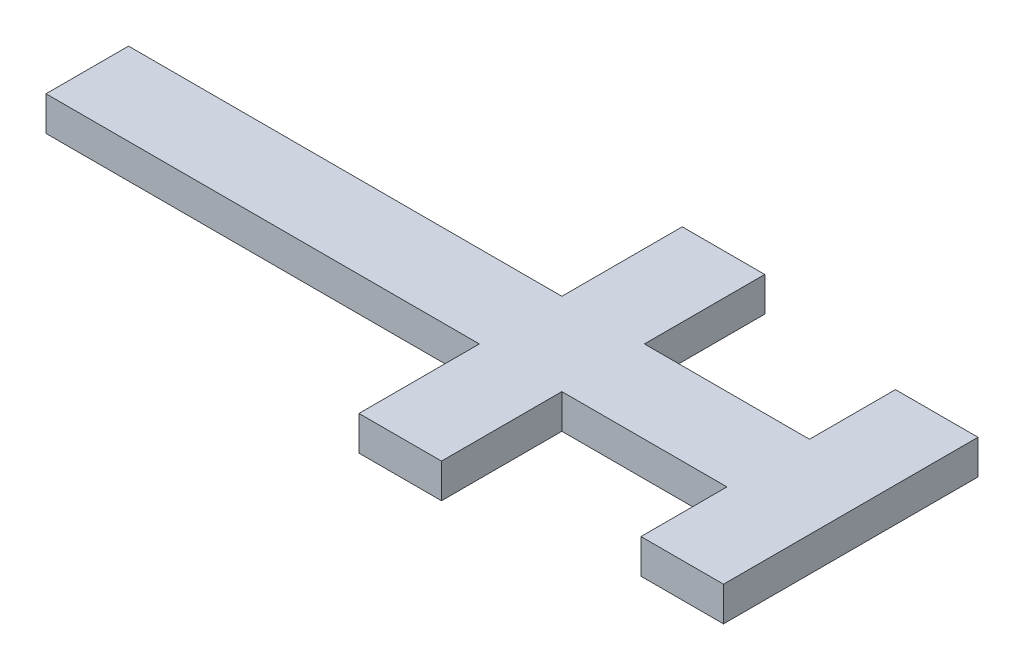
SolidWorks part; units mm, degrees
ref_plane "前视基准面" through (0, 0, 0) normal (0, 0, 1) x (1, 0, 0)
ref_plane "上视基准面" through (0, 0, 0) normal (0, 1, 0) x (1, 0, 0)
ref_plane "右视基准面" through (0, 0, 0) normal (1, 0, 0) x (0, 0, -1)
other "Configuration Table"
sketch "草图2" plane through (0, 0, 0) normal (0, 1, 0) x (1, 0, 0)
  line L0 (0, 0) -> (-40, 0) construction
  line L5 (-14, -5) -> (14, -5)
  line L6 (-14, -5) -> (-14, 5)
  line L7 (-14, 5) -> (14, 5)
  line L8 (14, -5) -> (14, 5)
  line L9 (-14, -5) -> (14, 5) construction
  line L10 (-14, 5) -> (14, -5) construction
  line L11 (19, 0) -> (14, 0) construction
  line L12 (-20, -5) -> (-60, -5)
  line L13 (-20, -5) -> (-20, 5)
  line L14 (-20, 5) -> (-60, 5)
  line L15 (-60, -5) -> (-60, 5)
  line L16 (-20, -5) -> (-60, 5) construction
  line L17 (-20, 5) -> (-60, -5) construction
  line L18 (-12, -22.5) -> (-22, -22.5)
  line L19 (-12, -22.5) -> (-12, 22.5)
  line L20 (-12, 22.5) -> (-22, 22.5)
  line L21 (-22, -22.5) -> (-22, 22.5)
  line L22 (-12, -22.5) -> (-22, 22.5) construction
  line L23 (-12, 22.5) -> (-22, -22.5) construction
  line L24 (24, -17.5) -> (14, -17.5)
  line L25 (24, -17.5) -> (24, 17.5)
  line L26 (24, 17.5) -> (14, 17.5)
  line L27 (14, -17.5) -> (14, 17.5)
  line L28 (24, -17.5) -> (14, 17.5) construction
  line L29 (24, 17.5) -> (14, -17.5) construction
  line L31 (-60, 5) -> (-85, 5)
  line L32 (-60, 5) -> (-60, -5)
  line L33 (-60, -5) -> (-85, -5)
  line L34 (-85, 5) -> (-85, -5)
  point P0 (0, 0)
  point P13 (19, 0)
  point P15 (-17, 0)
  dimension "D1" = 10
  dimension "D2" = 28
  dimension "D3" = 40
  dimension "D4" = 10
  dimension "D5" = 40
  dimension "D6" = 10
  dimension "D7" = 3
  dimension "D8" = 45
  dimension "D9" = 10
  dimension "D10" = 5
  dimension "D11" = 35
  dimension "D12" = 25
sketch "草图3" plane through (0, 0, 0) normal (0, 1, 0) x (1, 0, 0)
  line L0 (-14, -5) -> (14, -5) construction
  line L1 (24, 17.5) -> (14, 17.5)
  line L2 (24, 17.5) -> (24, -17.5)
  line L3 (24, -17.5) -> (14, -17.5)
  line L4 (14, 17.5) -> (14, -17.5)
  line L5 (14, 5) -> (-12, 5)
  line L6 (14, 5) -> (14, -5)
  line L7 (14, -5) -> (-12, -5)
  line L8 (-12, 5) -> (-12, -5)
  line L9 (-12, -22.5) -> (-12, 22.5) construction
  line L10 (-20, 5) -> (-60, 5) construction
  line L11 (-12, 22.5) -> (-22, 22.5)
  line L12 (-12, 22.5) -> (-12, -22.5)
  line L13 (-12, -22.5) -> (-22, -22.5)
  line L14 (-22, 22.5) -> (-22, -22.5)
  line L15 (-60, -5) -> (-22, -5)
  line L16 (-60, -5) -> (-60, 5)
  line L17 (-60, 5) -> (-22, 5)
  line L18 (-22, -5) -> (-22, 5)
  line L20 (-60, 5) -> (-85, 5)
  line L21 (-60, 5) -> (-60, -5)
  line L22 (-60, -5) -> (-85, -5)
  line L23 (-85, 5) -> (-85, -5)
extrude "凸台-拉伸1" add sketch "草图3" along normal blind 1 contours L1 L4 L3 L2 | L5 L8 L7 L4 | L11 L14 L13 L12 L8 | L17 L16 L15 L14 | L20 L23 L22 L16
sketch "草图4" plane through (0, 0, 0) normal (0, -1, 0) x (1, 0, 0)
  line L0 (13, -18.5) -> (25, -18.5)
  line L1 (25, -18.5) -> (25, 18.5)
  line L2 (25, 18.5) -> (13, 18.5)
  line L3 (13, 18.5) -> (13, 6)
  line L4 (13, 6) -> (-11, 6)
  line L5 (-11, 6) -> (-11, 23.5)
  line L6 (-11, 23.5) -> (-23, 23.5)
  line L7 (-23, 23.5) -> (-23, 6)
  line L8 (-23, 6) -> (-86, 6)
  line L9 (-86, 6) -> (-86, -6)
  line L10 (-86, -6) -> (-23, -6)
  line L11 (-23, -6) -> (-23, -23.5)
  line L12 (-23, -23.5) -> (-11, -23.5)
  line L13 (-11, -23.5) -> (-11, -6)
  line L14 (-11, -6) -> (13, -6)
  line L15 (13, -6) -> (13, -18.5)
  line L16 (14, -17.5) -> (24, -17.5)
  line L17 (24, -17.5) -> (24, 17.5)
  line L18 (24, 17.5) -> (14, 17.5)
  line L19 (14, 17.5) -> (14, 5)
  line L20 (14, 5) -> (-12, 5)
  line L21 (-12, 5) -> (-12, 22.5)
  line L22 (-12, 22.5) -> (-22, 22.5)
  line L23 (-22, 22.5) -> (-22, 5)
  line L24 (-22, 5) -> (-85, 5)
  line L25 (-85, 5) -> (-85, -5)
  line L26 (-85, -5) -> (-22, -5)
  line L27 (-22, -5) -> (-22, -22.5)
  line L28 (-22, -22.5) -> (-12, -22.5)
  line L29 (-12, -22.5) -> (-12, -5)
  line L30 (-12, -5) -> (14, -5)
  line L31 (14, -5) -> (14, -17.5)
  line L32 (14, -17.5) -> (24, -17.5)
  line L33 (24, -17.5) -> (24, 17.5)
  line L34 (24, 17.5) -> (14, 17.5)
  line L35 (14, 17.5) -> (14, 5)
  line L36 (14, 5) -> (-12, 5)
  line L37 (-12, 5) -> (-12, 22.5)
  line L38 (-12, 22.5) -> (-22, 22.5)
  line L39 (-22, 22.5) -> (-22, 5)
  line L40 (-22, 5) -> (-85, 5)
  line L41 (-85, 5) -> (-85, -5)
  line L42 (-85, -5) -> (-22, -5)
  line L43 (-22, -5) -> (-22, -22.5)
  line L44 (-22, -22.5) -> (-12, -22.5)
  line L45 (-12, -22.5) -> (-12, -5)
  line L46 (-12, -5) -> (14, -5)
  line L47 (14, -5) -> (14, -17.5)
  dimension "D1" = 0
  dimension "D2" = 1
extrude "凸台-拉伸2" add sketch "草图4" along normal blind 4 and the other way blind 1
sketch "草图5" plane through (0, 0, 0) normal (0, -1, 0) x (1, 0, 0)
  line L0 (-22, 22.5) -> (-22, 5)
  line L1 (-85, 5) -> (-60, 5)
  line L2 (-85, 5) -> (-85, -5)
  line L3 (-85, -5) -> (-60, -5)
  line L4 (-60, 5) -> (-60, -5)
  line L5 (14, 17.5) -> (24, 17.5)
  line L6 (14, 17.5) -> (14, -17.5)
  line L7 (14, -17.5) -> (24, -17.5)
  line L8 (24, 17.5) -> (24, -17.5)
  line L9 (-22, 5) -> (-20, 5)
  line L10 (-20, 5) -> (-20, -5)
  line L11 (-20, -5) -> (-22, -5)
  line L12 (-22, -5) -> (-22, -22.5)
  line L13 (-22, -22.5) -> (-12, -22.5)
  line L14 (-12, -22.5) -> (-12, -5)
  line L15 (-12, -5) -> (-14, -5)
  line L16 (-14, -5) -> (-14, 5)
  line L17 (-14, 5) -> (-12, 5)
  line L18 (-12, 5) -> (-12, 22.5)
  line L19 (-12, 22.5) -> (-22, 22.5)
extrude "凸台-拉伸3" add sketch "草图5" along normal blind 2
